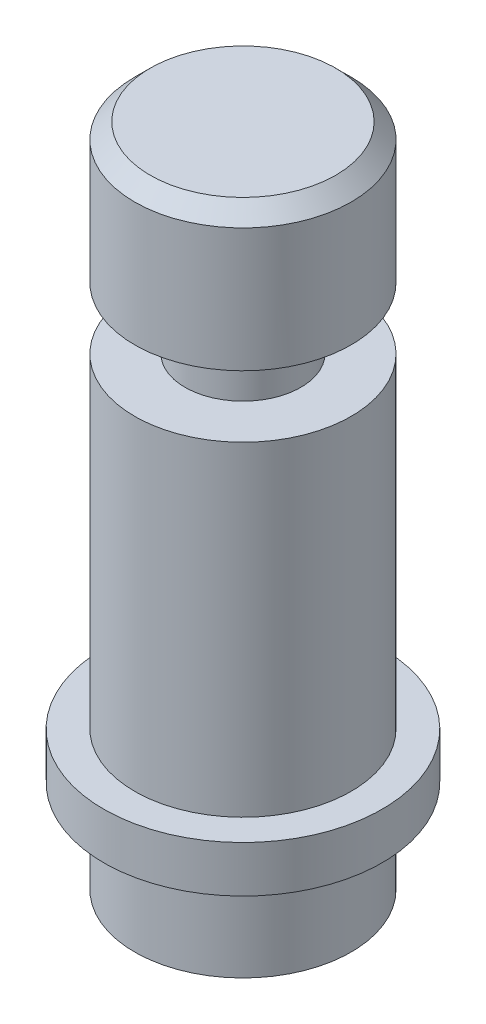
SolidWorks part; units mm, degrees
ref_plane "Front Plane" through (0, 0, 0) normal (0, 0, 1) x (1, 0, 0)
ref_plane "Top Plane" through (0, 0, 0) normal (0, 1, 0) x (1, 0, 0)
ref_plane "Right Plane" through (0, 0, 0) normal (1, 0, 0) x (0, 0, -1)
sketch "Sketch1" plane through (0, 0, 0) normal (0, 0, 1) x (1, 0, 0)
  line L0 (0, 0) -> (7, 0)
  line L1 (7, 0) -> (7, 6)
  line L2 (7, 6) -> (9, 6)
  line L3 (9, 6) -> (9, 9)
  line L4 (9, 9) -> (7, 9)
  line L5 (7, 9) -> (7, 30)
  line L6 (7, 30) -> (3.75, 30)
  line L7 (3.75, 30) -> (3.75, 34)
  line L8 (3.75, 34) -> (7, 34)
  line L9 (7, 34) -> (7, 43)
  line L10 (7, 43) -> (0, 43)
  line L11 (0, 43) -> (0, 0)
  point P12 (9, 7.5)
  dimension "D1" = 7
  dimension "D2" = 9
  dimension "D3" = 3.75
  dimension "D4" = 43
  dimension "D5" = 9
  dimension "D6" = 4
  dimension "D7" = 25
  dimension "D8" = 3
  dimension "D9" = 6
revolve "Revolve1" add sketch "Sketch1" angle 360 about L11
chamfer "Chamfer1" distance 1 angle 45 1 edges at (-7, 43, 0)
